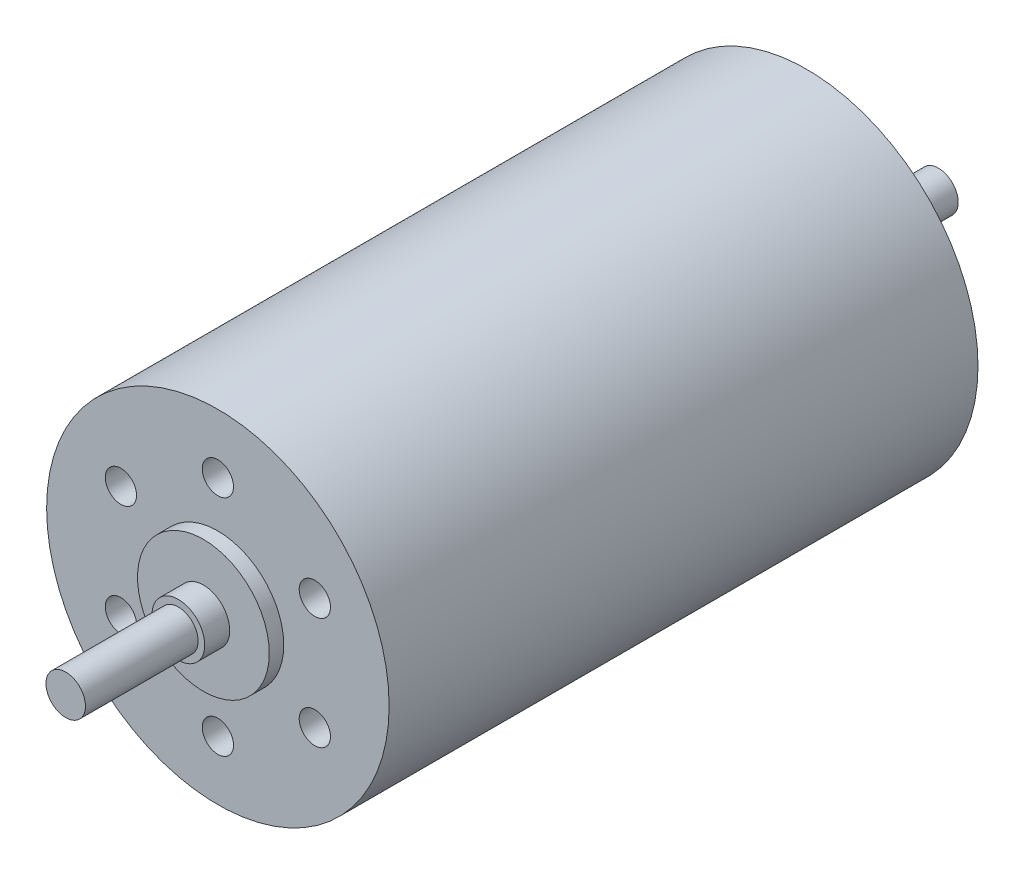
SolidWorks part; units mm, degrees
ref_plane "Front Plane" through (0, 0, 0) normal (1, 0, 0) x (0, 1, 0)
ref_plane "Top Plane" through (0, 0, 0) normal (0, 0, 1) x (0, 1, 0)
ref_plane "Right Plane" through (0, 0, 0) normal (0, 1, 0) x (-1, 0, 0)
sketch "Sketch1" plane through (0, 0, 0) normal (0, 0, 1) x (0, 1, 0)
  circle A0 centre (0, 0) radius 13
  dimension "D1" = 26
extrude "Boss-Extrude1" add sketch "Sketch1" along normal mid plane 44.7
sketch "Sketch2" plane through (0, 0, 22.35) normal (0, 0, 1) x (1, 0, 0)
  circle A0 centre (0, 0) radius 5
  dimension "D1" = 10
extrude "Boss-Extrude2" add sketch "Sketch2" along normal blind 1.1
sketch "Sketch3" plane through (0, 0, 23.45) normal (0, 0, 1) x (1, 0, 0)
  circle A0 centre (0, 0) radius 2
  dimension "D1" = 4
extrude "Boss-Extrude3" add sketch "Sketch3" along normal blind 1.9
sketch "Sketch4" plane through (0, 0, 25.35) normal (0, 0, 1) x (1, 0, 0)
  circle A0 centre (0, 0) radius 1.5
  dimension "D1" = 3
extrude "Boss-Extrude4" add sketch "Sketch4" along normal blind 8.55
sketch "Sketch5" plane through (0, 0, -22.35) normal (0, 0, -1) x (1, 0, 0)
  circle A0 centre (0, 0) radius 4
  dimension "D1" = 8
extrude "Boss-Extrude5" add sketch "Sketch5" along normal blind 2.2
sketch "Sketch6" plane through (0, 0, -24.55) normal (0, 0, -1) x (1, 0, 0)
  circle A0 centre (0, 0) radius 1.5
  dimension "D1" = 3
extrude "Boss-Extrude6" add sketch "Sketch6" along normal blind 7.8
hole_wizard "#42 (0.0935) Diameter Hole1" positions "Sketch8" profile "Sketch9" hole size "#42" standard "ANSI Inch"
sketch "Sketch8" plane through (0, 0, 22.35) normal (0, 0, 1) x (1, 0, 0)
  line L0 (-7.3612, 4.25) -> (7.3612, -4.25) construction
  line L2 (7.3612, 4.25) -> (-7.3612, -4.25) construction
  line L4 (0, 8.5) -> (0, -8.5) construction
  circle A0 centre (0, 0) radius 8.5
  point P0 (7.3612, -4.25)
  point P2 (0, 8.5)
  point P4 (-7.3612, 4.25)
  point P6 (-7.3612, -4.25)
  point P8 (7.3612, 4.25)
  point P10 (0, -8.5)
  point P37 (8.5, 0)
  point P38 (0, 0)
  point P39 (9.161, 0)
  point P40 (0, 0)
  point P41 (0, 0)
  point P42 (9.5059, 0)
  point P43 (6.0104, -6.0104)
  point P44 (-7.3612, -4.25)
  point P45 (7.3612, 4.25)
  dimension "D1" = 17
  dimension "D2" = 60
  dimension "D3" = 60
sketch "Sketch9" plane through (7.3612, -4.25, 22.35) normal (1, 0, 0) x (0, -1, 0)
  line L0 (0, 0) -> (0, 13.4135)
  line L1 (0, 13.4135) -> (1.1874, 12.7)
  line L2 (1.1874, 12.7) -> (1.1874, 0)
  line L5 (1.1874, 0) -> (0, 0)
  line L10 (0, 13.4135) -> (-1.1874, 12.7) construction
  line L11 (0, -6.35) -> (0, 107.95) construction
  dimension "Hole Dia." = 2.3749
  dimension "Hole Depth" = 12.7
  dimension "Drill Angle" = 118
